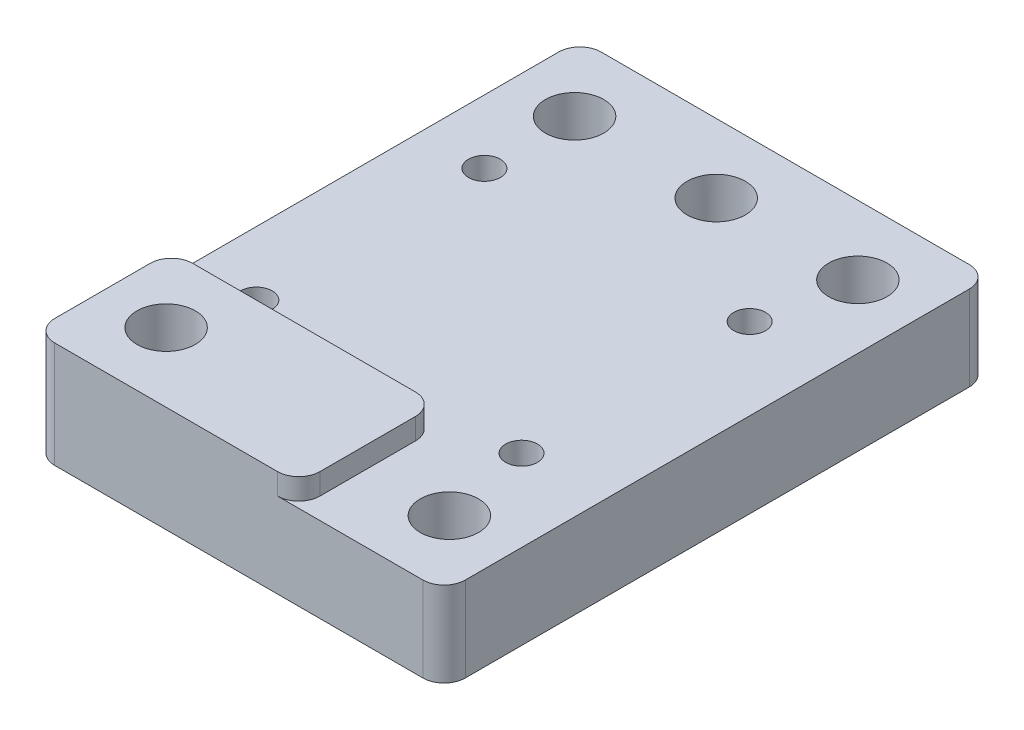
SolidWorks part; units mm, degrees
ref_plane "Front Plane" through (0, 0, 0) normal (0, 0, 1) x (1, 0, 0)
ref_plane "Top Plane" through (0, 0, 0) normal (0, 1, 0) x (1, 0, 0)
ref_plane "Right Plane" through (0, 0, 0) normal (1, 0, 0) x (0, 0, -1)
sketch "Sketch1" plane through (0, 0, 0) normal (0, 1, 0) x (1, 0, 0)
  line L1 (-19.35, -25.75) -> (19.35, -25.75)
  line L2 (-19.35, -25.75) -> (-19.35, 25.75)
  line L3 (-19.35, 25.75) -> (19.35, 25.75)
  line L4 (19.35, -25.75) -> (19.35, 25.75)
  line L5 (-19.35, -25.75) -> (19.35, 25.75) construction
  line L6 (-19.35, 25.75) -> (19.35, -25.75) construction
  point P0 (0, 0)
  dimension "D1" = 51.5
  dimension "D2" = 38.7
extrude "Boss-Extrude1" add sketch "Sketch1" along normal blind 8
sketch "Sketch2" plane through (0, 8, 0) normal (0, 1, 0) x (1, 0, 0)
  line L0 (-5.5, 0) -> (5.5, 0) construction
  line L2 (19.35, -25.75) -> (19.35, 25.75) construction
  circle A0 centre (11.65, 10.75) radius 1.5
  circle A1 centre (-13.35, 10.75) radius 1.5
  dimension "D1" = 3
  dimension "D4" = 3
  dimension "D2" = 10.75
  dimension "D3" = 7.7
  dimension "D5" = 25
extrude "Cut-Extrude1" cut sketch "Sketch2" against normal through all
mirror "Mirror1" about plane through (0, 0, 0) normal (0, 0, 1) of "Cut-Extrude1"
sketch "Sketch6" plane through (0, 8, 0) normal (0, 1, 0) x (1, 0, 0)
  line L1 (5.65, -12.75) -> (-19.35, -12.75)
  line L2 (5.65, -12.75) -> (5.65, -25.75)
  line L3 (5.65, -25.75) -> (-19.35, -25.75)
  line L4 (-19.35, -12.75) -> (-19.35, -25.75)
  circle A0 centre (-13.35, -10.75) radius 1.5 construction
  dimension "D1" = 2
  dimension "D2" = 25
  dimension "D3" = 13
extrude "Boss-Extrude3" add sketch "Sketch6" along normal blind 2
sketch "Sketch3" plane through (0, 8, 0) normal (0, 1, 0) x (1, 0, 0)
  line L0 (19.35, -25.75) -> (19.35, 25.75) construction
  line L1 (-5.5, 0) -> (5.5, 0) construction
  circle A0 centre (13.35, -19.25) radius 2.75
  dimension "D1" = 5.5
  dimension "D2" = 6
  dimension "D3" = 19.25
extrude "Cut-Extrude2" cut sketch "Sketch3" against normal through all both and the other way through all
mirror "Mirror2" about plane through (0, 0, 0) normal (1, 0, 0) of "Cut-Extrude2"
mirror "Mirror3" about plane through (0, 0, 0) normal (0, 0, 1) of "Mirror2", "Cut-Extrude2"
sketch "Sketch4" plane through (0, 8, 0) normal (0, 1, 0) x (1, 0, 0)
  line L3 (-5.5, 0) -> (5.5, 0) construction
  line L4 (0, -5.5) -> (0, 5.5) construction
  circle A0 centre (0, 19.25) radius 2.75
  dimension "D1" = 5.5
  dimension "D3" = 19.25
extrude "Cut-Extrude3" cut sketch "Sketch4" against normal through all both and the other way through all
fillet "Fillet1" radius 2 3 edges at (5.65, 9, 25.75) (-19.35, 9, 12.75) (5.65, 9, 12.75)
fillet "Fillet2" radius 2 4 edges at (-19.35, 4, -25.75) (19.35, 4, -25.75) (19.35, 4, 25.75) (-19.35, 5, 25.75)
